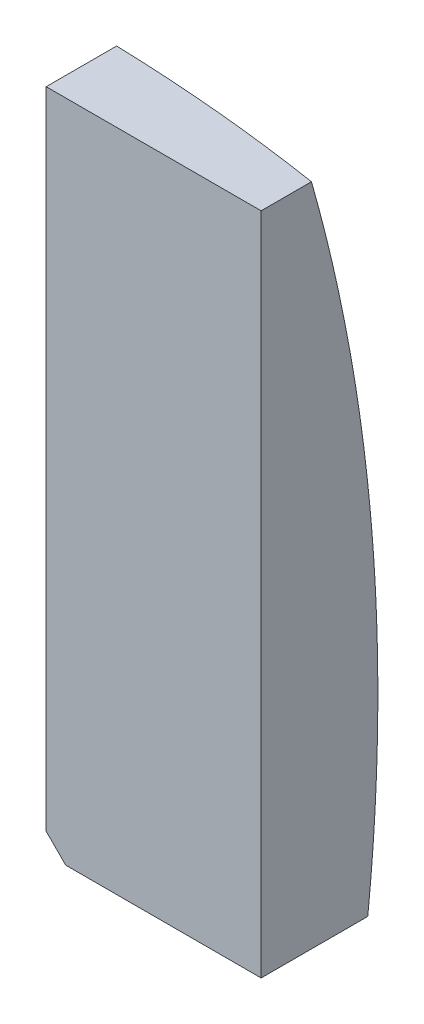
SolidWorks part; units mm, degrees
material "Стекло"
ref_plane "Спереди" through (0, 0, 0) normal (0, 0, 1) x (1, 0, 0)
ref_plane "Сверху" through (0, 0, 0) normal (0, 1, 0) x (1, 0, 0)
ref_plane "Справа" through (0, 0, 0) normal (1, 0, 0) x (0, 0, -1)
sketch "Эскиз1" plane through (0, 0, 0) normal (0, 1, 0) x (1, 0, 0)
  line L0 (0, 3.5) -> (0, 0) construction
  line L1 (0, 3.5) -> (18, 3.5) construction
  line L2 (14, 0) -> (14, 1.2767)
  line L3 (0, 0) -> (14, 0)
  line L4 (0, 3.5) -> (0, 0)
  arc A0 (0, 3.5) -> (14, 1.2767) centre (0, -41.69) cw
  dimension "D3" = 45.19
  dimension "D1" = 3.5
  dimension "D2" = 14
revolve "Повернуть1" add sketch "Эскиз1" angle 360 about L4
sketch "Эскиз2" plane through (0, 0, 0) normal (0, 0, 1) x (1, 0, 0)
  line L0 (0, 14) -> (0, -14) construction
  line L1 (1.3, 12.2) -> (6.8, 12.2)
  line L2 (1.3, 12.2) -> (1.3, -4.8)
  line L3 (1.3, -4.8) -> (6.8, -4.8)
  line L4 (6.8, 12.2) -> (6.8, -4.8)
  line L5 (-6.8, 12.2) -> (-6.8, -4.8)
  line L6 (-1.3, -4.8) -> (-6.8, -4.8)
  line L7 (-1.3, 12.2) -> (-1.3, -4.8)
  line L8 (-1.3, 12.2) -> (-6.8, 12.2)
  circle A0 centre (0, 0) radius 14 construction
  point P4 (3.3, 2.7)
  dimension "D1" = 5.5
  dimension "D2" = 17
  dimension "D3" = 2.7
  dimension "D4" = 3.3
  dimension "D5" = 2
  dimension "D6" = 7.5
extrude "Вырез-Вытянуть1" cut sketch "Эскиз2" against normal through all flip side to cut contours L4 L1 L2 L3
chamfer "Фаска2" [suppressed] distance 0.25 angle 45
chamfer "Фаска3" distance 0.5 angle 45 1 edges at (1.3, -4.8, -1.6128)
